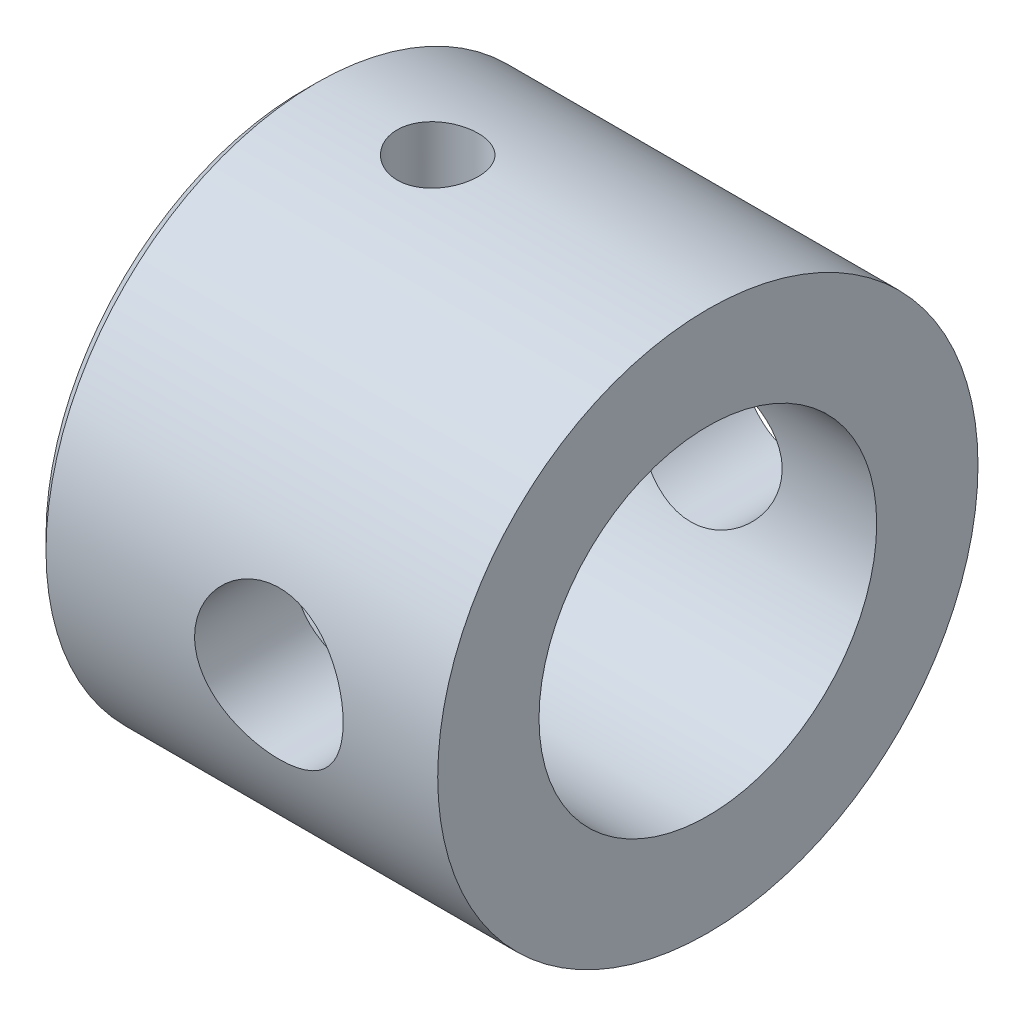
SolidWorks part; units mm, degrees
material "AISI 304"
ref_plane "Front Plane" through (0, 0, 0) normal (0, 0, 1) x (1, 0, 0)
ref_plane "Top Plane" through (0, 0, 0) normal (0, 1, 0) x (1, 0, 0)
ref_plane "Right Plane" through (0, 0, 0) normal (1, 0, 0) x (0, 0, -1)
sketch "Sketch1" plane through (0, 0, 0) normal (0, 0, 1) x (1, 0, 0)
  line L0 (0, 0) -> (60, 0) construction
  line L1 (2, 40) -> (60, 40)
  line L2 (60, 40) -> (60, 25)
  line L3 (60, 25) -> (2, 25)
  line L4 (0, 27) -> (0, 38)
  line L5 (2, 25) -> (0, 27)
  line L6 (0, 38) -> (2, 40)
  point P3 (0, 40)
  point P7 (0, 25)
  dimension "D1" = 60
  dimension "D2" = 80
  dimension "D3" = 50
  dimension "D4" = 2
  dimension "D5" = 45
  dimension "D6" = 2
  dimension "D7" = 45
revolve "Revolve1" add sketch "Sketch1" angle 360 about L0
sketch "Sketch2" plane through (0, 0, 0) normal (0, 1, 0) x (1, 0, 0)
  line L0 (0, 38) -> (0, -38) construction
  circle A0 centre (20, 0) radius 6
  dimension "D1" = 12
  dimension "D2" = 20
extrude "Cut-Extrude1" cut sketch "Sketch2" against normal through all and the other way through all
sketch "Sketch3" plane through (0, 0, 0) normal (0, 0, 1) x (1, 0, 0)
  line L0 (0, 38) -> (0, -38) construction
  circle A0 centre (35, 0) radius 11
  dimension "D1" = 22
  dimension "D2" = 35
extrude "Cut-Extrude2" cut sketch "Sketch3" against normal through all both and the other way through all
